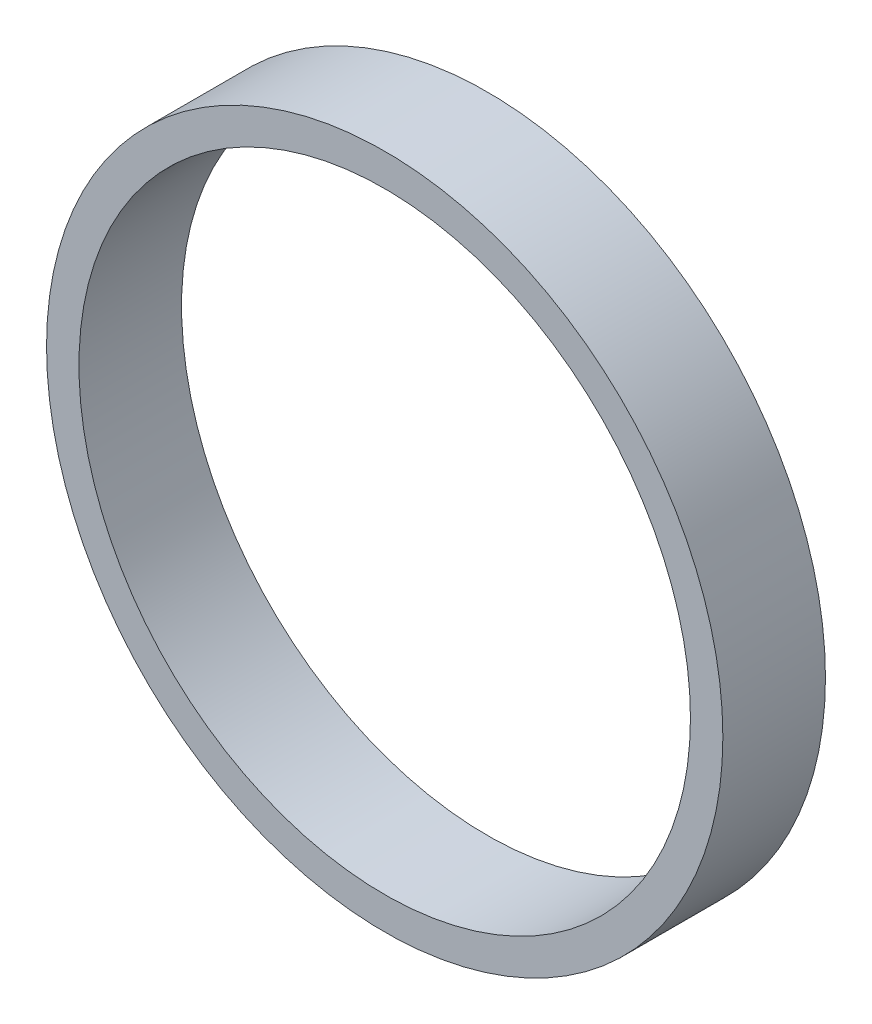
SolidWorks part; units mm, degrees
material "Copper"
ref_plane "Front Plane" through (0, 0, 0) normal (0, 0, 1) x (1, 0, 0)
ref_plane "Top Plane" through (0, 0, 0) normal (0, 1, 0) x (1, 0, 0)
ref_plane "Right Plane" through (0, 0, 0) normal (1, 0, 0) x (0, 0, -1)
sketch "Sketch1" plane through (0, 0, 0) normal (0, 0, 1) x (1, 0, 0)
  circle A0 centre (0, 0) radius 56.769
  circle A1 centre (0, 0) radius 62.7888
extrude "Boss-Extrude1" add sketch "Sketch1" along normal blind 19.05
